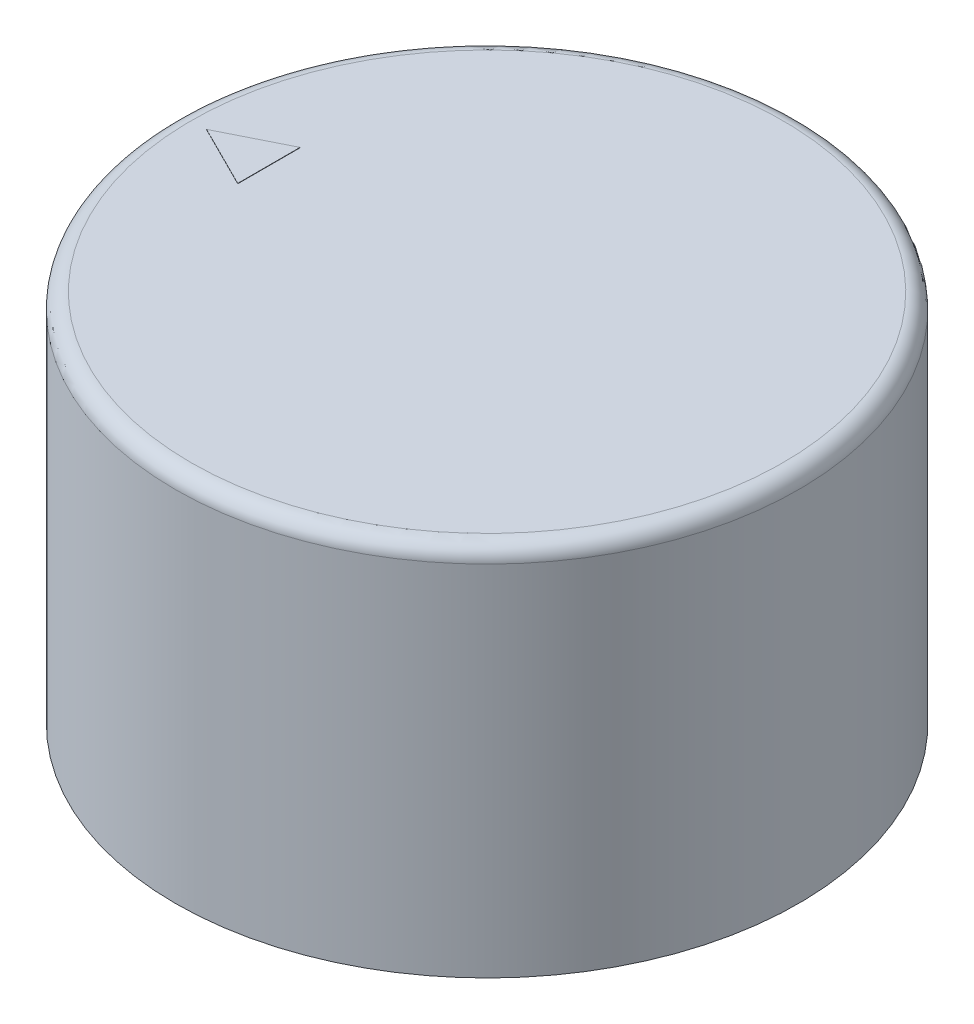
SolidWorks part; units mm, degrees
ref_plane "Front Plane" through (0, 0, 0) normal (0, 0, 1) x (1, 0, 0)
ref_plane "Top Plane" through (0, 0, 0) normal (0, 1, 0) x (1, 0, 0)
ref_plane "Right Plane" through (0, 0, 0) normal (1, 0, 0) x (0, 0, -1)
sketch "Sketch1" plane through (0, 0, 0) normal (0, 1, 0) x (1, 0, 0)
  circle A0 centre (0, 0) radius 10
  dimension "D1" = 20
extrude "Boss-Extrude1" add sketch "Sketch1" along normal blind 12
fillet "Fillet1" radius 0.5 1 edges at (0, 12, 10)
sketch "Sketch2" plane through (0, 0, 0) normal (0, -1, 0) x (1, 0, 0)
  circle A0 centre (0, 0) radius 3
  dimension "D1" = 6
extrude "Cut-Extrude1" cut sketch "Sketch2" against normal offset from surface (10 mm away) 2 up to face at (0, 12, 9.5)
sketch "Sketch3" plane through (0, 12, 0) normal (0, 1, 0) x (1, 0, 0)
  line L0 (0, 0) -> (-9, 0) construction
  line L1 (-9, 0) -> (-7, -1)
  line L2 (-7, -1) -> (-7, 1)
  line L3 (-7, 1) -> (-9, 0)
  line L4 (-9, 0) -> (-9.5, 0) construction
  circle A1 centre (0, 0) radius 9.5 construction
  point P6 (-7, 0)
  dimension "D1" = 2
  dimension "D2" = 2
  dimension "D3" = 0.5
extrude "Boss-Extrude2" add sketch "Sketch3" along normal blind 0.01 contours L2 L3 L1
